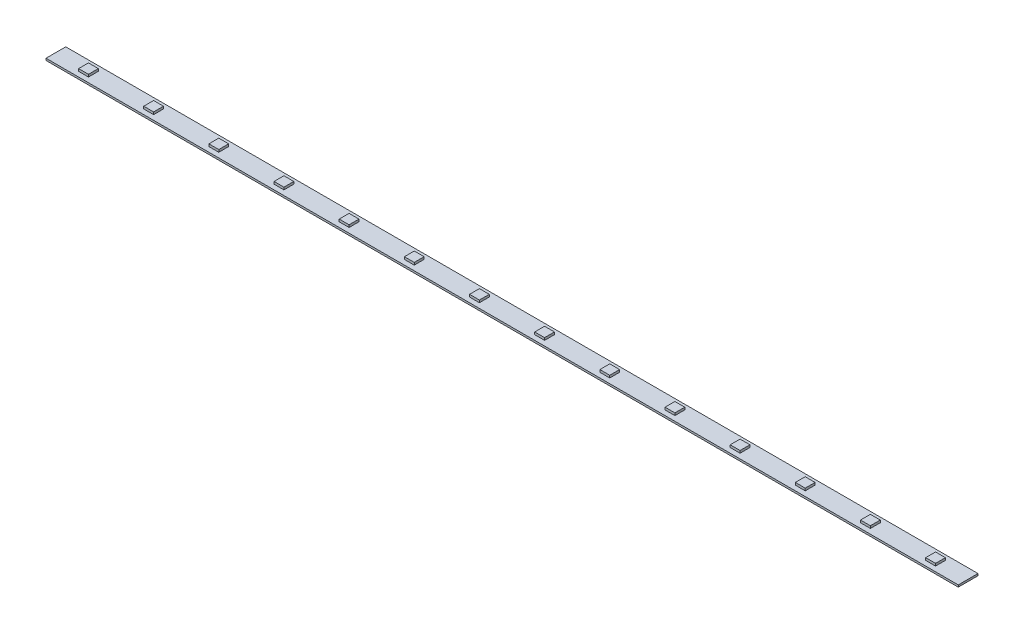
SolidWorks part; units mm, degrees
ref_plane "Ebene vorne" through (0, 0, 0) normal (0, 0, 1) x (1, 0, 0)
ref_plane "Ebene oben" through (0, 0, 0) normal (0, 1, 0) x (1, 0, 0)
ref_plane "Ebene rechts" through (0, 0, 0) normal (1, 0, 0) x (0, 0, -1)
sketch "Sketch1" plane through (0, 0, 0) normal (0, 1, 0) x (1, 0, 0)
  line L1 (-16.5, -5) -> (16.5, -5)
  line L2 (-16.5, -5) -> (-16.5, 5)
  line L3 (-16.5, 5) -> (16.5, 5)
  line L4 (16.5, -5) -> (16.5, 5)
  line L5 (-16.5, -5) -> (16.5, 5) construction
  line L6 (-16.5, 5) -> (16.5, -5) construction
  point P0 (0, 0)
  dimension "D1" = 33
  dimension "D2" = 10
extrude "Boss-Extrude1" add sketch "Sketch1" along normal blind 1
sketch "Sketch3" plane through (0, 1, 0) normal (0, 1, 0) x (1, 0, 0)
  line L1 (-2.5, -2.5) -> (2.5, -2.5)
  line L2 (-2.5, -2.5) -> (-2.5, 2.5)
  line L3 (-2.5, 2.5) -> (2.5, 2.5)
  line L4 (2.5, -2.5) -> (2.5, 2.5)
  line L5 (-2.5, -2.5) -> (2.5, 2.5) construction
  line L6 (-2.5, 2.5) -> (2.5, -2.5) construction
  point P0 (0, 0)
  dimension "D1" = 5
  dimension "D2" = 5
extrude "Boss-Extrude2" add sketch "Sketch3" along normal blind 1.2
pattern_linear "LPattern1" count 8 spacing 33 along (-1, 0, 0) count 7 spacing 33 along (1, 0, 0) of "Boss-Extrude1", "Boss-Extrude2"
